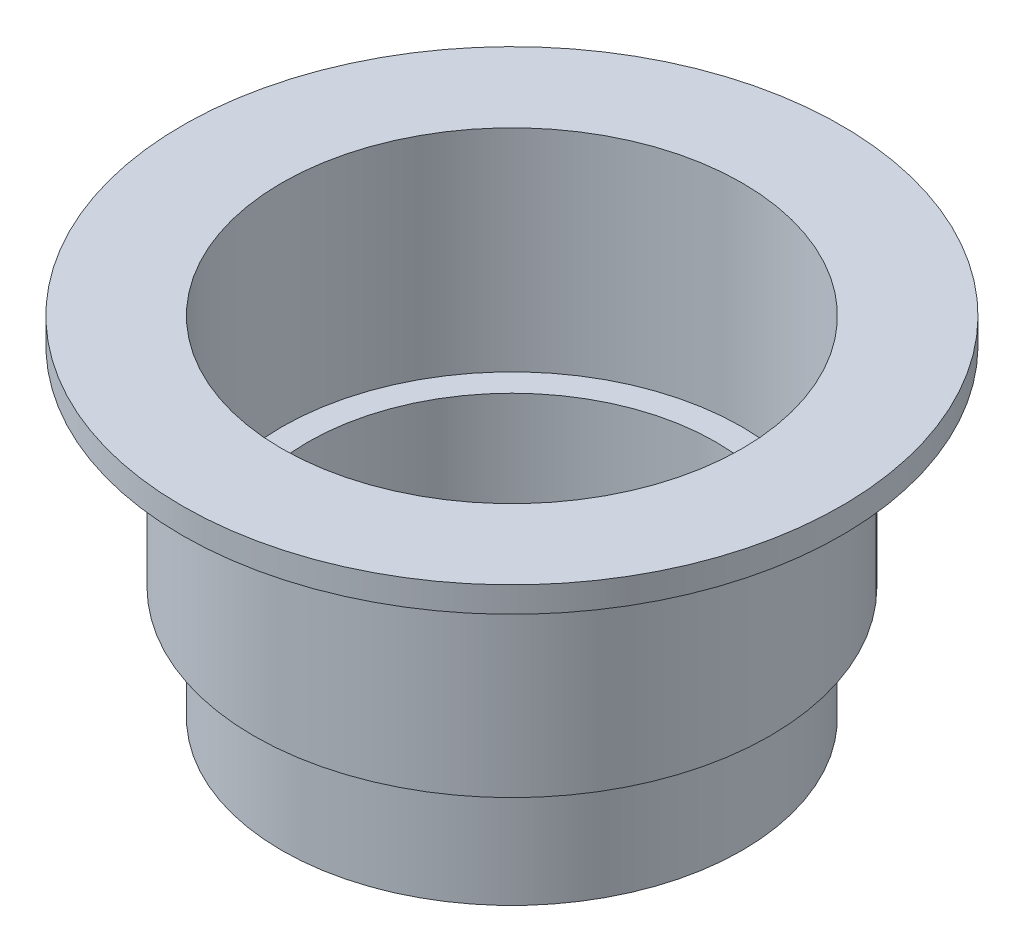
SolidWorks part; units mm, degrees
ref_plane "前视基准面" through (0, 0, 0) normal (0, 0, 1) x (1, 0, 0)
ref_plane "上视基准面" through (0, 0, 0) normal (0, 1, 0) x (1, 0, 0)
ref_plane "右视基准面" through (0, 0, 0) normal (1, 0, 0) x (0, 0, -1)
sketch "草图1" plane through (0, 0, 0) normal (0, 1, 0) x (1, 0, 0)
  circle A0 centre (0, 0) radius 24.725
  circle A1 centre (0, 0) radius 31.5
  circle A2 centre (0, 0) radius 22.11
  dimension "D1" = 49.45
  dimension "D2" = 63
  dimension "D3" = 44.22
sketch "草图2" plane through (0, 0, 0) normal (0, 0, 1) x (1, 0, 0)
  line L0 (31.5, 0) -> (-31.5, 0) construction
  line L2 (22, 0) -> (31.5, 0)
  line L3 (22, 0) -> (22, -2.44)
  line L4 (22, -2.44) -> (31.5, -2.44)
  line L5 (31.5, 0) -> (31.5, -2.44)
  line L6 (0, 6.9355) -> (0, -41.5579) construction
  line L7 (22, -2.44) -> (24.665, -2.44)
  line L8 (22, -2.44) -> (22, -22.45)
  line L9 (22, -22.45) -> (24.665, -22.45)
  line L10 (24.665, -2.44) -> (24.665, -22.45)
  line L11 (22, -20.2) -> (19.5, -20.2)
  line L12 (22, -20.2) -> (22, -33.26)
  line L13 (22, -33.26) -> (19.5, -33.26)
  line L14 (19.5, -20.2) -> (19.5, -33.26)
  line L15 (19.5, -33.26) -> (0, -33.26)
  line L16 (19.5, -33.26) -> (19.5, -33.16)
  line L17 (19.5, -33.16) -> (0, -33.16)
  line L18 (0, -33.26) -> (0, -33.16)
  dimension "D1" = 2.44
  dimension "D2" = 9.5
  dimension "D3" = 31.5
  dimension "D4" = 22.45
  dimension "D5" = 2.665
  dimension "D6" = 20.2
  dimension "D7" = 33.26
  dimension "D8" = 2.5
  dimension "D9" = 0.1
revolve "旋转1" add sketch "草图2" angle 360 about L6
